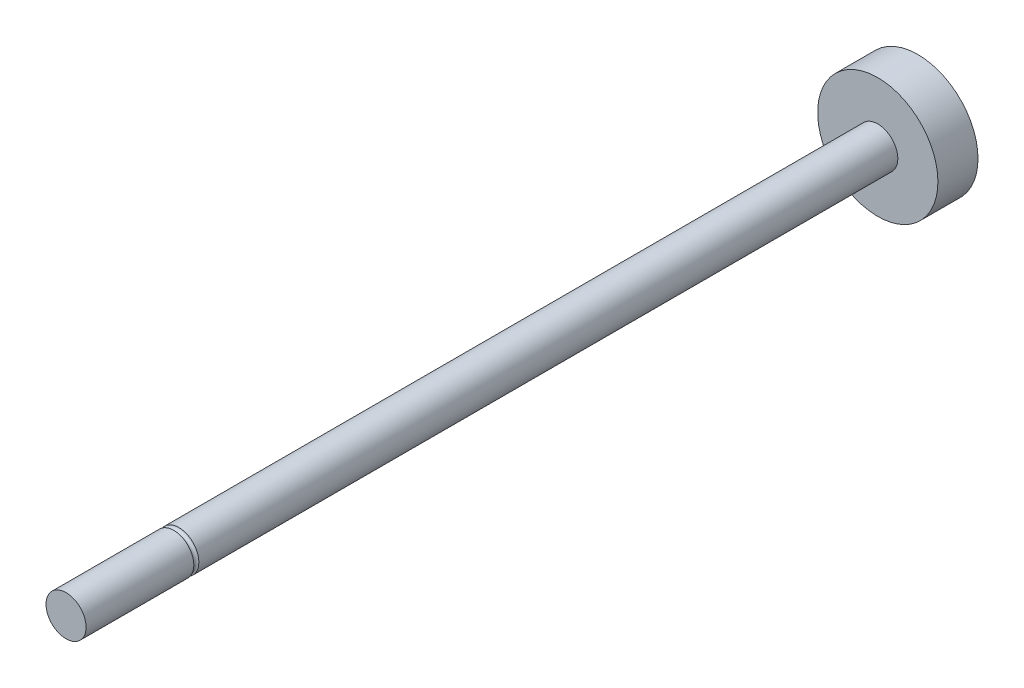
SolidWorks part; units mm, degrees
ref_plane "Front Plane" through (0, 0, 0) normal (0, 0, 1) x (1, 0, 0)
ref_plane "Top Plane" through (0, 0, 0) normal (0, 1, 0) x (1, 0, 0)
ref_plane "Right Plane" through (0, 0, 0) normal (1, 0, 0) x (0, 0, -1)
sketch "Sketch1" plane through (0, 0, 0) normal (0, 0, 1) x (1, 0, 0)
  circle A0 centre (0, 0) radius 6
  dimension "D1" = 12
extrude "Boss-Extrude1" add sketch "Sketch1" along normal blind 4
sketch "Sketch2" plane through (0, 0, 0) normal (0, 0, 1) x (1, 0, 0)
  circle A0 centre (0, 0) radius 2
  dimension "D1" = 4
extrude "Boss-Extrude2" add sketch "Sketch2" along normal blind 85
sketch "Sketch3" plane through (0, 0, 0) normal (1, 0, 0) x (0, 0, -1)
  line L0 (-4, 2) -> (-85, 2) construction
  line L1 (-85, 2) -> (-85, -2) construction
  line L2 (0, 0) -> (-85, 0) construction
  circle A0 centre (-74, 2) radius 0.25
  dimension "D1" = 0.5
  dimension "D2" = 11
revolve "Cut-Revolve1" cut sketch "Sketch3" angle 360 about L2
